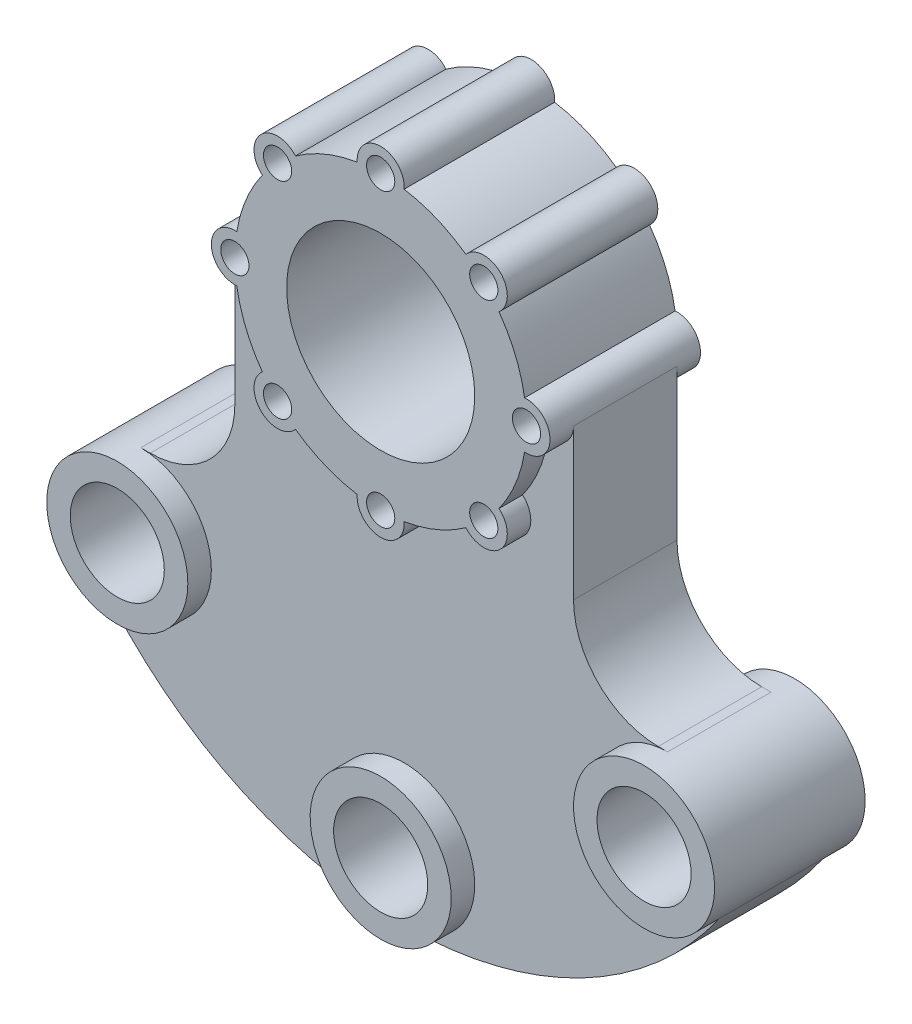
SolidWorks part; units mm, degrees
ref_plane "Front Plane" through (0, 0, 0) normal (0, 0, 1) x (1, 0, 0)
ref_plane "Top Plane" through (0, 0, 0) normal (0, 1, 0) x (1, 0, 0)
ref_plane "Right Plane" through (0, 0, 0) normal (1, 0, 0) x (0, 0, -1)
sketch "Sketch1" plane through (0, 0, 0) normal (0, 0, 1) x (1, 0, 0)
  line L0 (-36, 0) -> (-36, -32)
  line L1 (36, 0) -> (36, -32)
  line L3 (-54, -50) -> (-56, -50)
  line L5 (54, -50) -> (56, -50)
  arc A0 (-30.5968, -4.9837) -> (-25.1592, -18.1112) centre (0, 0) ccw
  circle A1 centre (0, 0) radius 20
  circle A2 centre (31, 0) radius 3
  arc A3 (30.5968, -4.9837) -> (30.5968, 4.9837) centre (31, 0) ccw
  arc A4 (18.1112, -25.1592) -> (25.1592, -18.1112) centre (21.9203, -21.9203) ccw
  circle A5 centre (21.9203, -21.9203) radius 3
  arc A6 (-4.9837, -30.5968) -> (4.9837, -30.5968) centre (0, -31) ccw
  circle A7 centre (0, -31) radius 3
  arc A8 (-25.1592, -18.1112) -> (-18.1112, -25.1592) centre (-21.9203, -21.9203) ccw
  circle A9 centre (-21.9203, -21.9203) radius 3
  arc A10 (-30.5968, 4.9837) -> (-30.5968, -4.9837) centre (-31, 0) ccw
  circle A11 centre (-31, 0) radius 3
  arc A12 (-18.1112, 25.1592) -> (-25.1592, 18.1112) centre (-21.9203, 21.9203) ccw
  circle A13 centre (-21.9203, 21.9203) radius 3
  arc A14 (4.9837, 30.5968) -> (-4.9837, 30.5968) centre (0, 31) ccw
  circle A15 centre (0, 31) radius 3
  arc A16 (25.1592, 18.1112) -> (18.1112, 25.1592) centre (21.9203, 21.9203) ccw
  circle A17 centre (21.9203, 21.9203) radius 3
  arc A18 (-18.1112, -25.1592) -> (-4.9837, -30.5968) centre (0, 0) ccw
  arc A19 (4.9837, -30.5968) -> (18.1112, -25.1592) centre (0, 0) ccw
  arc A20 (25.1592, -18.1112) -> (30.5968, -4.9837) centre (0, 0) ccw
  arc A21 (30.5968, 4.9837) -> (25.1592, 18.1112) centre (0, 0) ccw
  arc A22 (18.1112, 25.1592) -> (4.9837, 30.5968) centre (0, 0) ccw
  arc A23 (-4.9837, 30.5968) -> (-18.1112, 25.1592) centre (0, 0) ccw
  arc A24 (-25.1592, 18.1112) -> (-30.5968, 4.9837) centre (0, 0) ccw
  circle A25 centre (0, -95) radius 15
  circle A26 centre (0, -95) radius 10
  circle A27 centre (-56, -65) radius 15
  circle A28 centre (56, -65) radius 15
  circle A29 centre (-56, -65) radius 10
  circle A30 centre (56, -65) radius 10
  arc A31 (-67.7478, -74.3269) -> (66.2162, -75.9832) centre (-0.1851, -28.1843) ccw
  arc A32 (54, -50) -> (36, -32) centre (54, -32) cw
  arc A33 (-54, -50) -> (-36, -32) centre (-54, -32) ccw
  point P31 (0, 0)
  point P56 (36, -50)
  point P59 (-36, -50)
  dimension "D1" = 62
  dimension "D2" = 40
  dimension "D3" = 6
  dimension "D4" = 10
  dimension "D13" = 30
  dimension "D14" = 20
  dimension "D15" = 18
  dimension "D6" = 95
  dimension "D7" = 50
  dimension "D8" = 50
  dimension "D9" = 20
  dimension "D10" = 20
  dimension "D11" = 15
  dimension "D12" = 15
  dimension "D5" = 8
extrude "Boss-Extrude5" add sketch "Sketch1" along normal mid plane 32 contours A12 A24 A10 A0 A8 A18 A6 A19 A4 A20 A3 A21 A16 A22 A14 A23 A1 A2 A5 A7 A9 A11 A13 A15 A17 | A27 A29 | A25 A26 | A28 A30
sketch "Sketch2" plane through (0, 0, 16) normal (0, 0, 1) x (1, 0, 0)
  line L0 (-36, 0) -> (-36, -50)
  line L1 (-36, -50) -> (-56, -50)
  line L2 (36, 0) -> (36, -50)
  line L3 (36, -50) -> (56, -50)
  arc A0 (-30.5968, 4.9837) -> (-30.5968, -4.9837) centre (-31, 0) ccw construction
  circle A1 centre (-56, -65) radius 15 construction
  arc A2 (30.5968, -4.9837) -> (30.5968, 4.9837) centre (31, 0) ccw construction
  circle A3 centre (56, -65) radius 15 construction
  arc A4 (-56, -50) -> (-68.0677, -73.909) centre (-56, -65) ccw
  arc A5 (66.9898, -75.2091) -> (56, -50) centre (56, -65) ccw
  arc A6 (-68.0677, -73.909) -> (66.9898, -75.2091) centre (-0.0902, -27.9367) ccw
  arc A23 (-18.1112, 25.1592) -> (-25.1592, 18.1112) centre (-21.9203, 21.9203) ccw
  arc A24 (-25.1592, 18.1112) -> (-30.5968, 4.9837) centre (0, 0) ccw
  arc A25 (-30.5968, 4.9837) -> (-30.5968, -4.9837) centre (-31, 0) ccw
  arc A26 (-30.5968, -4.9837) -> (-25.1592, -18.1112) centre (0, 0) ccw
  arc A27 (-25.1592, -18.1112) -> (-18.1112, -25.1592) centre (-21.9203, -21.9203) ccw
  arc A28 (-18.1112, -25.1592) -> (-4.9837, -30.5968) centre (0, 0) ccw
  arc A29 (-4.9837, -30.5968) -> (4.9837, -30.5968) centre (0, -31) ccw
  arc A30 (4.9837, -30.5968) -> (18.1112, -25.1592) centre (0, 0) ccw
  arc A31 (18.1112, -25.1592) -> (25.1592, -18.1112) centre (21.9203, -21.9203) ccw
  arc A32 (25.1592, -18.1112) -> (30.5968, -4.9837) centre (0, 0) ccw
  arc A33 (30.5968, -4.9837) -> (30.5968, 4.9837) centre (31, 0) ccw
  arc A34 (30.5968, 4.9837) -> (25.1592, 18.1112) centre (0, 0) ccw
  arc A35 (25.1592, 18.1112) -> (18.1112, 25.1592) centre (21.9203, 21.9203) ccw
  arc A36 (18.1112, 25.1592) -> (4.9837, 30.5968) centre (0, 0) ccw
  arc A37 (4.9837, 30.5968) -> (-4.9837, 30.5968) centre (0, 31) ccw
  arc A38 (-4.9837, 30.5968) -> (-18.1112, 25.1592) centre (0, 0) ccw
  arc A41 (-30.5968, 4.9837) -> (-30.5968, -4.9837) centre (-31, 0) ccw
  arc A42 (-30.5968, -4.9837) -> (-25.1592, -18.1112) centre (0, 0) ccw
  arc A43 (-25.1592, -18.1112) -> (-18.1112, -25.1592) centre (-21.9203, -21.9203) ccw
  arc A44 (-18.1112, -25.1592) -> (-4.9837, -30.5968) centre (0, 0) ccw
  arc A45 (-4.9837, -30.5968) -> (4.9837, -30.5968) centre (0, -31) ccw
  arc A46 (4.9837, -30.5968) -> (18.1112, -25.1592) centre (0, 0) ccw
  arc A47 (18.1112, -25.1592) -> (25.1592, -18.1112) centre (21.9203, -21.9203) ccw
  arc A48 (25.1592, -18.1112) -> (30.5968, -4.9837) centre (0, 0) ccw
  arc A49 (30.5968, -4.9837) -> (36, 0) centre (31, 0) ccw
  arc M28 (-30.5968, 4.9837) -> (-30.5968, -4.9837) centre (-31, 0) ccw
  arc M29 (-30.5968, -4.9837) -> (-25.1592, -18.1112) centre (0, 0) ccw
  arc M30 (-25.1592, -18.1112) -> (-18.1112, -25.1592) centre (-21.9203, -21.9203) ccw
  arc M31 (-18.1112, -25.1592) -> (-4.9837, -30.5968) centre (0, 0) ccw
  arc M32 (-4.9837, -30.5968) -> (4.9837, -30.5968) centre (0, -31) ccw
  arc M33 (4.9837, -30.5968) -> (18.1112, -25.1592) centre (0, 0) ccw
  arc M34 (18.1112, -25.1592) -> (25.1592, -18.1112) centre (21.9203, -21.9203) ccw
  arc M35 (25.1592, -18.1112) -> (30.5968, -4.9837) centre (0, 0) ccw
  arc M36 (30.5968, -4.9837) -> (30.5968, 4.9837) centre (31, 0) ccw
  dimension "D4" = 82.0634
  dimension "D2" = 20
  dimension "D3" = 20
  dimension "D1" = 0
extrude "Boss-Extrude6" add sketch "Sketch2" against normal blind 22 from offset 5 contours A4 A6 A5 L3 L2 L0 L1 M36 M35 M34 M33 M32 M31 M30 M29 M28 offset against normal yes
sketch "Sketch3" plane through (0, 0, 11) normal (0, 0, 1) x (1, 0, 0)
  circle A0 centre (-56, -65) radius 10
  circle A1 centre (0, -95) radius 10
  circle A2 centre (56, -65) radius 10
extrude "Cut-Extrude1" cut sketch "Sketch3" against normal through all
fillet "Fillet1" radius 18 2 edges at (36, -50, 0) (-36, -50, 0)
